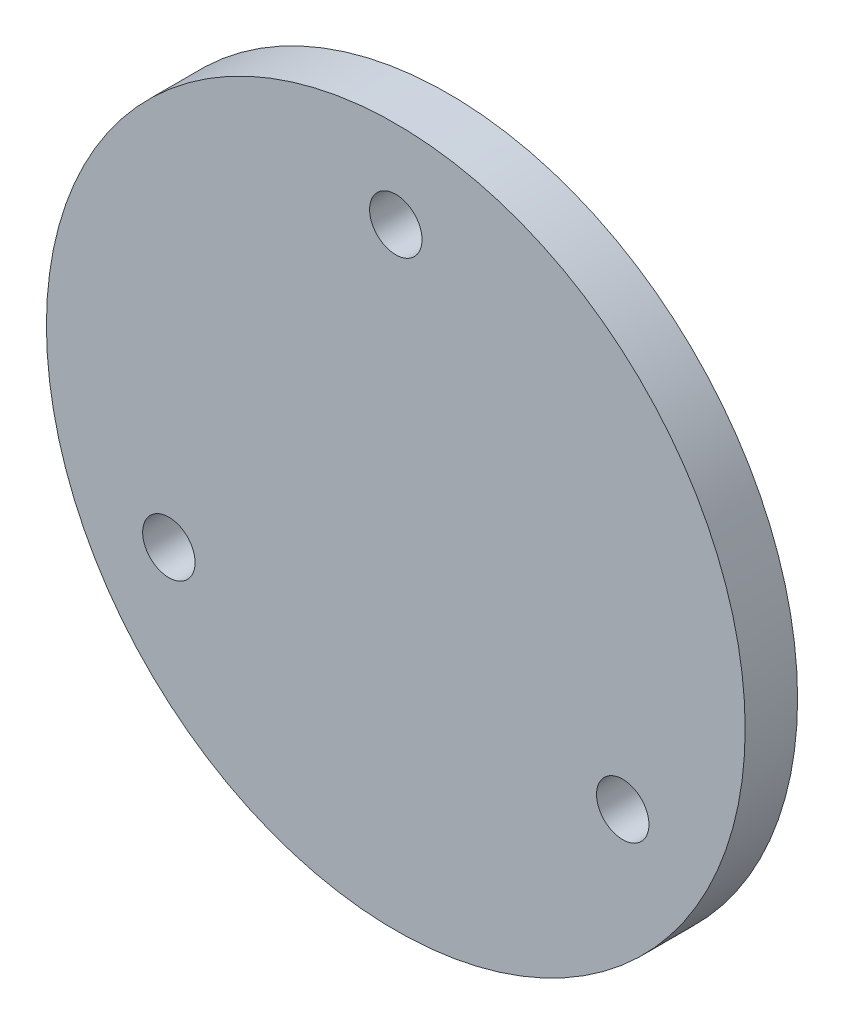
SolidWorks part; units mm, degrees
ref_plane "Front Plane" through (0, 0, 0) normal (0, 0, 1) x (1, 0, 0)
ref_plane "Top Plane" through (0, 0, 0) normal (0, 1, 0) x (1, 0, 0)
ref_plane "Right Plane" through (0, 0, 0) normal (1, 0, 0) x (0, 0, -1)
sketch "Sketch1" plane through (0, 0, 0) normal (0, 0, 1) x (1, 0, 0)
  line L0 (0, 0) -> (0, 16.7239) construction
  line L1 (0, 0) -> (-17.6898, -10.2132) construction
  line L2 (0, 0) -> (15.3438, -8.8588) construction
  circle A0 centre (0, 0) radius 20
  circle A1 centre (0, 15) radius 1.5
  circle A2 centre (-12.9904, -7.5) radius 1.5
  circle A3 centre (12.9904, -7.5) radius 1.5
  dimension "D1" = 40
  dimension "D4" = 3
  dimension "D6" = 3
  dimension "D8" = 3
  dimension "D2" = 120
  dimension "D3" = 120
  dimension "D5" = 15
  dimension "D7" = 15
  dimension "D9" = 15
extrude "Boss-Extrude1" add sketch "Sketch1" along normal blind 3 contours A0 | A2 | A1 | A3
